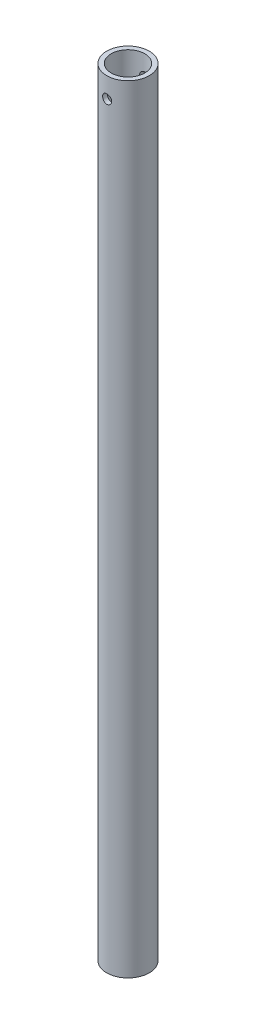
SolidWorks part; units mm, degrees
material "6061 Alloy"
ref_plane "Front Plane" through (0, 0, 0) normal (0, 0, 1) x (1, 0, 0)
ref_plane "Top Plane" through (0, 0, 0) normal (0, 1, 0) x (1, 0, 0)
ref_plane "Right Plane" through (0, 0, 0) normal (1, 0, 0) x (0, 0, -1)
sketch "Sketch2" plane through (0, 0, 0) normal (1, 0, 0) x (0, 0, -1)
  line L0 (0, 0) -> (0, 609.6)
  dimension "D1" = 609.6
sweep "Sweep1" add path "Sketch2" circular profile diameter 33.401 parameters "D3"=33.401
shell "Shell1" thickness 3.556
ref_plane "Plane1" through (0, 0, 16.7005) normal (0, 0, 1) x (1, 0, 0)
sketch "Sketch21" plane through (0, 0, 16.7005) normal (0, 0, 1) x (1, 0, 0)
  line L0 (13.1445, 609.6) -> (-13.1445, 609.6) construction
  point P0 (0, 593.725)
  dimension "D1" = 15.875
hole_wizard "1/4 Clearance Hole4" positions "Sketch24" profile "Sketch25" hole size "1/4" standard "ANSI Inch" end condition through all
sketch "Sketch24" plane through (0, 0, 16.7005) normal (0, 0, 1) x (1, 0, 0)
  point P0 (0, 593.725)
sketch "Sketch25" plane through (0, 593.725, 16.7005) normal (1, 0, 0) x (0, -1, 0)
  line L0 (0, 0) -> (0, 33.401)
  line L1 (0, 33.401) -> (3.5712, 33.401)
  line L2 (3.5712, 33.401) -> (3.5712, 0)
  line L5 (3.5712, 0) -> (0, 0)
  line L11 (0, -6.35) -> (0, 107.95) construction
  dimension "Thru Hole Dia." = 7.1425
  dimension "Thru Hole Depth" = 33.401
